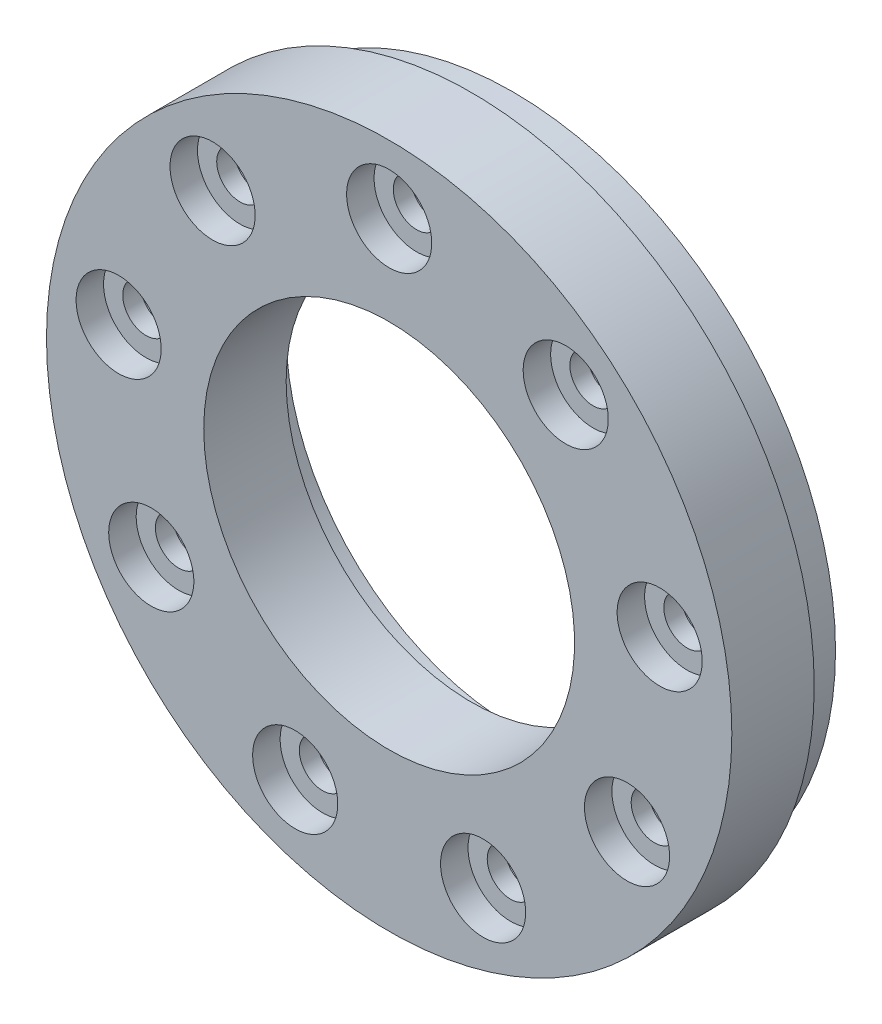
SolidWorks part; units mm, degrees
material "ABS"
ref_plane "Plan de face" through (0, 0, 0) normal (0, 0, 1) x (1, 0, 0)
ref_plane "Plan de dessus" through (0, 0, 0) normal (0, 1, 0) x (1, 0, 0)
ref_plane "Plan de droite" through (0, 0, 0) normal (1, 0, 0) x (0, 0, -1)
sketch "Esquisse1" plane through (0, 0, 0) normal (0, 0, 1) x (1, 0, 0)
  circle A0 centre (0, 0) radius 24.95
  dimension "D1" = 49.9
extrude "Boss.-Extru.1" add sketch "Esquisse1" along normal blind 6
sketch "Esquisse3" plane through (0, 0, 6) normal (0, 0, -1) x (-1, 0, 0)
  circle A0 centre (0, 0) radius 20 construction
  circle A1 centre (0, 20) radius 3.1
  circle A2 centre (12.8558, 15.3209) radius 3.1
  circle A3 centre (19.6962, 3.473) radius 3.1
  circle A4 centre (17.3205, -10) radius 3.1
  circle A5 centre (6.8404, -18.7939) radius 3.1
  circle A6 centre (-6.8404, -18.7939) radius 3.1
  circle A7 centre (-17.3205, -10) radius 3.1
  circle A8 centre (-19.6962, 3.473) radius 3.1
  circle A9 centre (-12.8558, 15.3209) radius 3.1
  point P23 (0, 0)
  dimension "D1" = 6.2
  dimension "D3" = 40
  dimension "D2" = 9
extrude "Enlèv. mat.-Extru.1" cut sketch "Esquisse3" along normal blind 2
sketch "Esquisse4" plane through (0, 0, 0) normal (0, 0, -1) x (-1, 0, 0)
  circle A0 centre (0, 0) radius 20 construction
  circle A1 centre (0, 20) radius 1.7
  circle A2 centre (12.8558, 15.3209) radius 1.7
  circle A3 centre (19.6962, 3.473) radius 1.7
  circle A4 centre (17.3205, -10) radius 1.7
  circle A5 centre (6.8404, -18.7939) radius 1.7
  circle A6 centre (-6.8404, -18.7939) radius 1.7
  circle A7 centre (-17.3205, -10) radius 1.7
  circle A8 centre (-19.6962, 3.473) radius 1.7
  circle A9 centre (-12.8558, 15.3209) radius 1.7
  point P23 (0, 0)
  dimension "D1" = 40
  dimension "D2" = 3.4
  dimension "D3" = 9
extrude "Enlèv. mat.-Extru.2" cut sketch "Esquisse4" against normal through all
sketch "Esquisse5" plane through (0, 0, 0) normal (0, 0, -1) x (-1, 0, 0)
  circle A0 centre (0, 0) radius 16.5
  circle A1 centre (0, 0) radius 23.5
  circle A2 centre (-12.8558, 15.3209) radius 1.7 construction
  circle A3 centre (-19.6962, 3.473) radius 1.7 construction
  circle A4 centre (-17.3205, -10) radius 1.7 construction
  circle A5 centre (-6.8404, -18.7939) radius 1.7 construction
  circle A6 centre (6.8404, -18.7939) radius 1.7 construction
  circle A7 centre (17.3205, -10) radius 1.7 construction
  circle A8 centre (19.6962, 3.473) radius 1.7 construction
  circle A9 centre (12.8558, 15.3209) radius 1.7 construction
  circle A10 centre (0, 20) radius 1.7 construction
  circle A11 centre (-12.8558, 15.3209) radius 1.7
  circle A12 centre (-19.6962, 3.473) radius 1.7
  circle A13 centre (-17.3205, -10) radius 1.7
  circle A14 centre (-6.8404, -18.7939) radius 1.7
  circle A15 centre (6.8404, -18.7939) radius 1.7
  circle A16 centre (17.3205, -10) radius 1.7
  circle A17 centre (19.6962, 3.473) radius 1.7
  circle A18 centre (12.8558, 15.3209) radius 1.7
  circle A19 centre (0, 20) radius 1.7
  dimension "D1" = 33
  dimension "D2" = 47
extrude "Boss.-Extru.2" add sketch "Esquisse5" along normal blind 3
sketch "Esquisse6" plane through (0, 0, -3) normal (0, 0, -1) x (-1, 0, 0)
  circle A0 centre (12.8558, 15.3209) radius 2.1
  circle A1 centre (19.6962, 3.473) radius 2.1
  circle A2 centre (17.3205, -10) radius 2.1
  circle A3 centre (6.8404, -18.7939) radius 2.1
  circle A4 centre (-6.8404, -18.7939) radius 2.1
  circle A5 centre (-17.3205, -10) radius 2.1
  circle A6 centre (-19.6962, 3.473) radius 2.1
  circle A7 centre (-12.8558, 15.3209) radius 2.1
  circle A8 centre (0, 20) radius 2.1
  point P21 (0, 0)
  dimension "D1" = 4.2
  dimension "D2" = 9
extrude "Enlèv. mat.-Extru.3" cut sketch "Esquisse6" against normal blind 5.7
sketch "Esquisse7" plane through (0, 0, 0) normal (0, 0, -1) x (-1, 0, 0)
  circle A0 centre (0, 0) radius 13.5
  dimension "D1" = 27
extrude "Enlèv. mat.-Extru.4" cut sketch "Esquisse7" against normal through all
